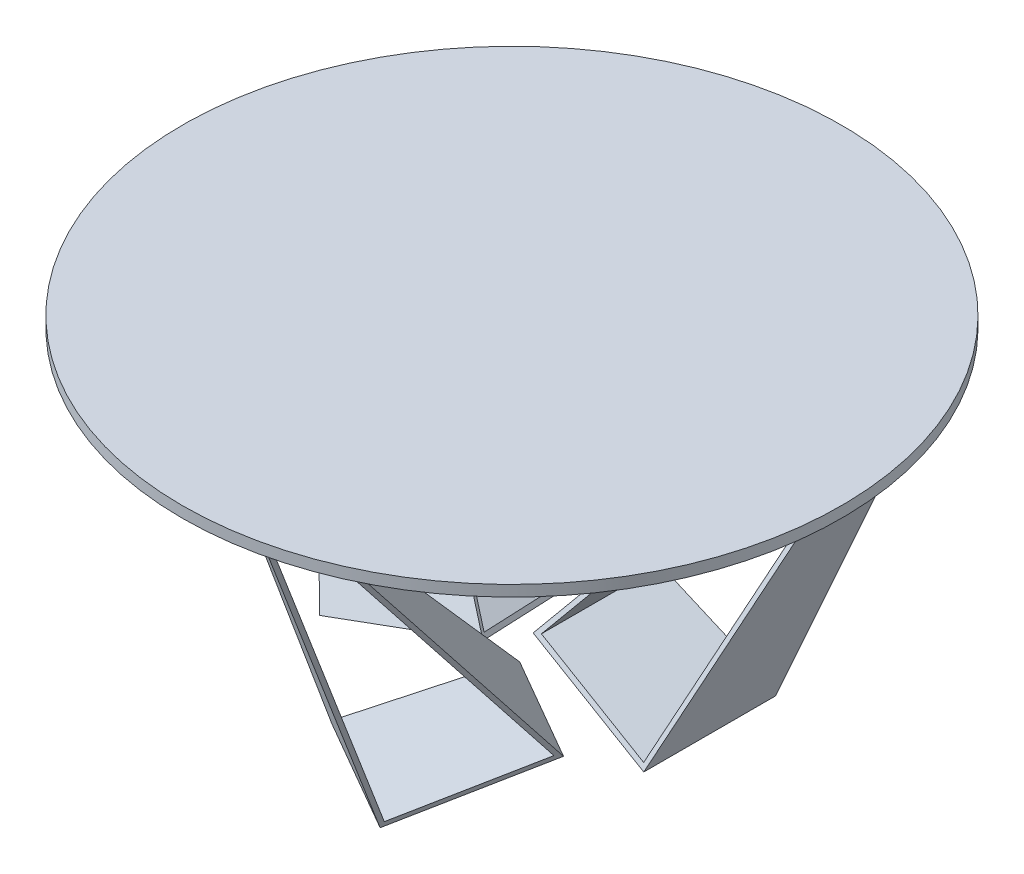
SolidWorks part; units mm, degrees
ref_plane "Alzado" through (0, 0, 0) normal (0, 0, 1) x (1, 0, 0)
ref_plane "Planta" through (0, 0, 0) normal (0, 1, 0) x (1, 0, 0)
ref_plane "Vista lateral" through (0, 0, 0) normal (1, 0, 0) x (0, 0, -1)
sketch "Croquis1" plane through (0, 0, 0) normal (0, 0, 1) x (1, 0, 0)
  line L0 (300, 0) -> (541.6667, 725)
  line L1 (541.6667, 725) -> (466.6667, 725)
  line L2 (466.6667, 725) -> (0, 100)
  line L3 (0, 100) -> (300, 0)
  dimension "D1" = 300
  dimension "D2" = 725
  dimension "D3" = 75
  dimension "D4" = 100
extrude "Saliente-Extruir1" add sketch "Croquis1" against normal blind 500
sketch "Croquis2" plane through (0, 0, 0) normal (1, 0, 0) x (0, 0, -1)
  line L0 (0, 0) -> (350, 725)
  line L1 (500, 725) -> (0, 725) construction
  line L2 (350, 725) -> (450, 725)
  line L3 (450, 725) -> (300, 0)
  line L4 (500, 0) -> (0, 0) construction
  line L5 (300, 0) -> (0, 0)
  dimension "D1" = 100
  dimension "D2" = 350
  dimension "D3" = 300
extrude "Cortar-Extruir2" cut sketch "Croquis2" against normal blind 50 and the other way blind 650 flip side to cut
shell "Vaciado2" thickness 10
sketch "Croquis4" plane through (0, 0, 0) normal (0, 0, 1) x (1, 0, 0)
  line L0 (0, 0) -> (0, 750) construction
pattern_circular "MatrizC1" count 3 over 360 about axis through (0, 0, 0) along (0, 1, 0) of bodies 103
sketch "Croquis5" plane through (0, 0, 0) normal (0, 1, 0) x (1, 0, 0)
  circle A0 centre (0, 0) radius 750
  dimension "D1" = 1500
extrude "Saliente-Extruir2" add sketch "Croquis5" along normal blind 25 from offset 725 separate body contours A0
